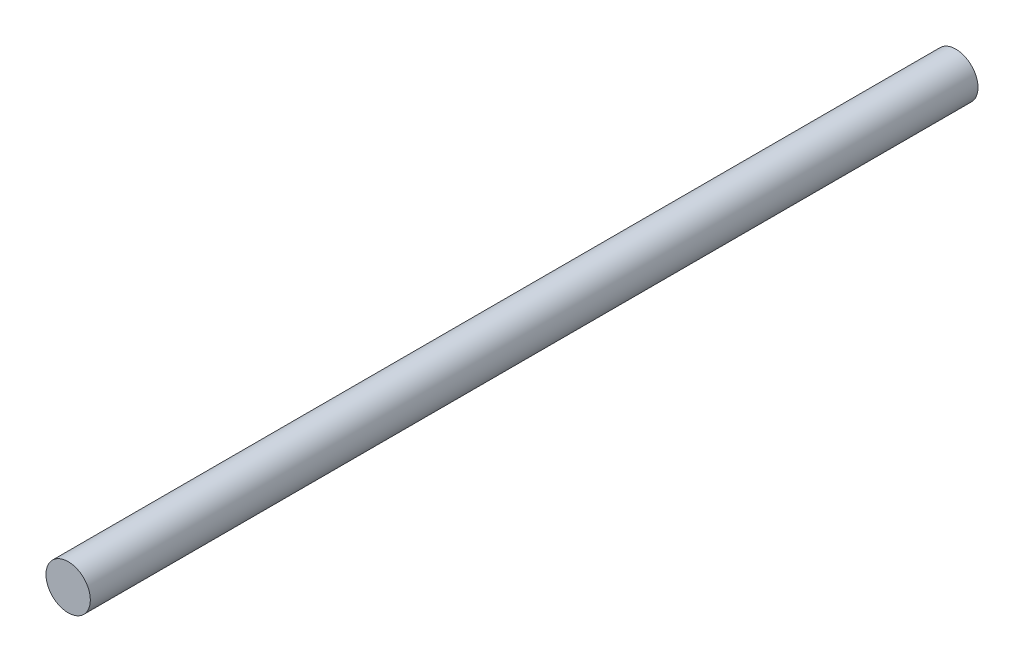
SolidWorks part; units mm, degrees
ref_plane "Alzado" through (0, 0, 0) normal (0, 0, 1) x (1, 0, 0)
ref_plane "Planta" through (0, 0, 0) normal (0, 1, 0) x (1, 0, 0)
ref_plane "Vista lateral" through (0, 0, 0) normal (1, 0, 0) x (0, 0, -1)
sketch "Croquis1" plane through (0, 0, 0) normal (0, 0, 1) x (1, 0, 0)
  circle A0 centre (0, 0) radius 1.5
  dimension "D1" = 3
extrude "Saliente-Extruir1" add sketch "Croquis1" along normal blind 60
